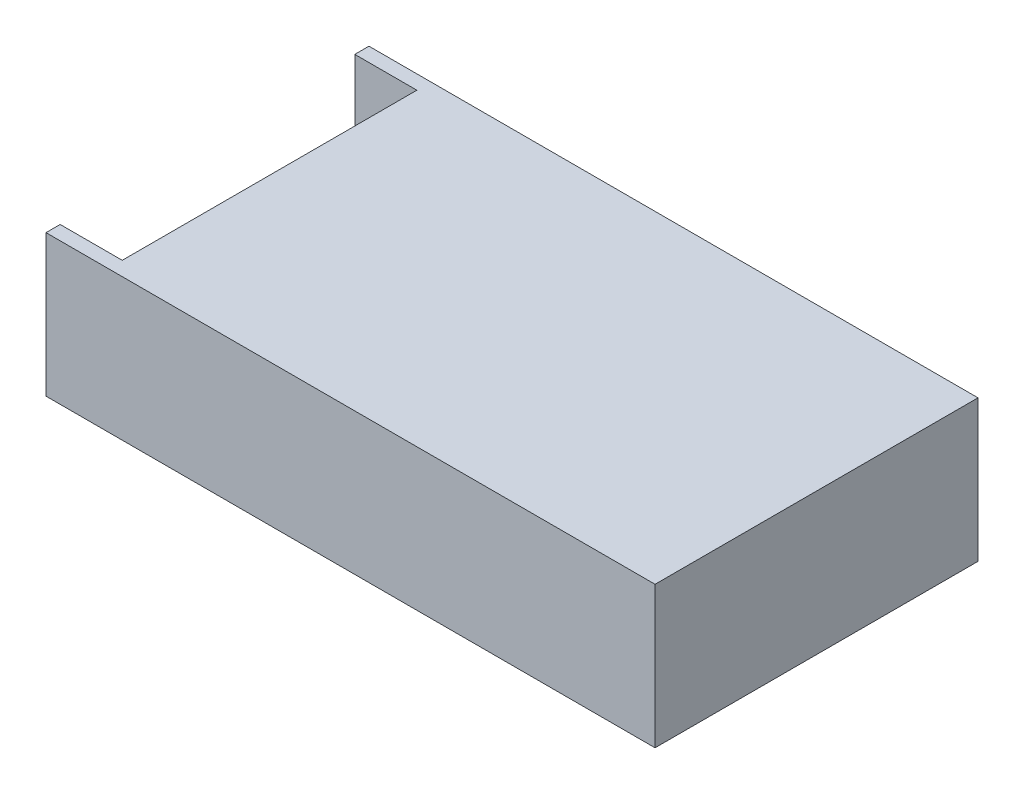
SolidWorks part; units mm, degrees
material "Liga 1060"
ref_plane "Plano frontal" through (0, 0, 0) normal (0, 0, 1) x (1, 0, 0)
ref_plane "Plano superior" through (0, 0, 0) normal (0, 1, 0) x (1, 0, 0)
ref_plane "Plano direito" through (0, 0, 0) normal (1, 0, 0) x (0, 0, -1)
sketch "Esboço1" plane through (0, 0, 0) normal (0, 1, 0) x (1, 0, 0)
  line L1 (-107.5, 57) -> (107.5, 57)
  line L2 (-107.5, 57) -> (-107.5, -57)
  line L3 (-107.5, -57) -> (107.5, -57)
  line L4 (107.5, 57) -> (107.5, -57)
  line L5 (-107.5, 57) -> (107.5, -57) construction
  line L6 (-107.5, -57) -> (107.5, 57) construction
  point P0 (0, 0)
  dimension "D1" = 215
  dimension "D2" = 114
extrude "Ressalto-extrusão1" add sketch "Esboço1" along normal blind 50
sketch "Esboço3" plane through (0, 0, 57) normal (0, 0, 1) x (1, 0, 0)
  line L1 (-107.5, 50) -> (-85.5852, 50)
  line L2 (-107.5, 50) -> (-107.5, 17.4571)
  line L3 (-102.4831, 16.1339) -> (-85.5852, 16.1339)
  line L4 (-85.5852, 50) -> (-85.5852, 16.1339)
  line L5 (-102.4831, 6.4269) -> (-107.5, 6.4269)
  line L6 (-102.4831, 6.4269) -> (-102.4831, 16.1339)
  line L8 (-107.5, 6.4269) -> (-107.5, 17.4571)
extrude "Corte-extrusão1" cut sketch "Esboço3" against normal offset from surface (104 mm away) 5 from offset 5 up to face at (0, 25, -57) offset against normal yes
sketch "Esboço4" plane through (0, 0, 0) normal (0, -1, 0) x (1, 0, 0)
  line L0 (107.5, 57) -> (107.5, -57) construction
  line L1 (-107.5, 57) -> (107.5, 57) construction
  circle A0 centre (96, 42) radius 2
  circle A1 centre (-29.6, 42) radius 2
  circle A2 centre (-29.6, -43) radius 2
  circle A3 centre (96, -43) radius 2
  dimension "D2" = 4
  dimension "D1" = 125.6
  dimension "D3" = 85
  dimension "D4" = 11.5
  dimension "D5" = 15
extrude "Corte-extrusão2" cut sketch "Esboço4" against normal blind 10
